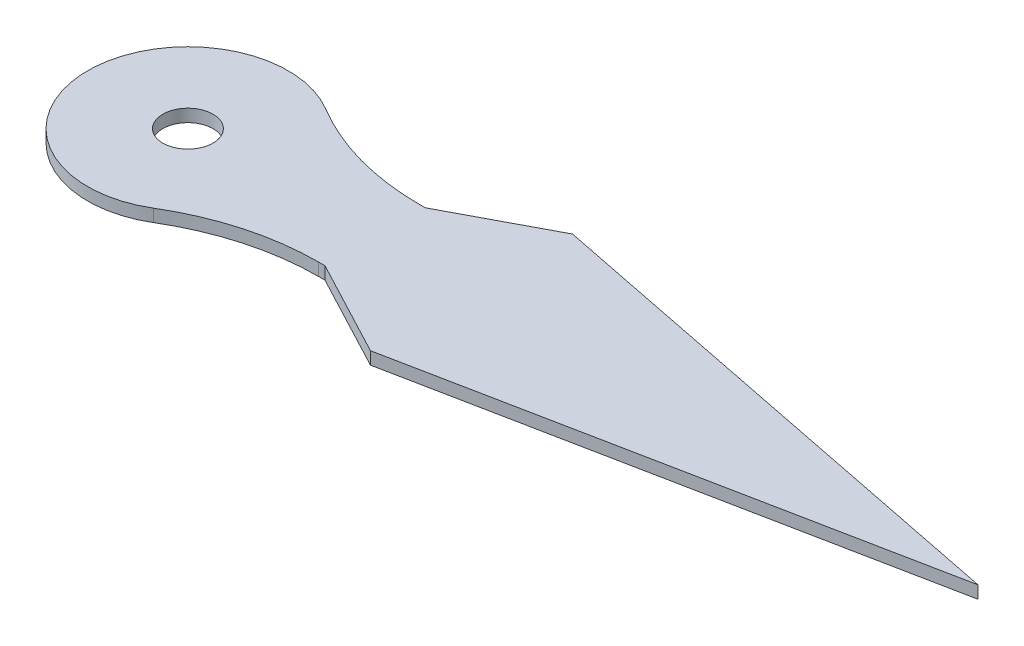
SolidWorks part; units mm, degrees
ref_plane "Front Plane" through (0, 0, 0) normal (0, 0, 1) x (1, 0, 0)
ref_plane "Top Plane" through (0, 0, 0) normal (0, 1, 0) x (1, 0, 0)
ref_plane "Right Plane" through (0, 0, 0) normal (1, 0, 0) x (0, 0, -1)
sketch "Sketch1" plane through (0, 0, 0) normal (0, 1, 0) x (1, 0, 0)
  line L3 (3.4641, 2) -> (7.4641, 2)
  line L4 (11.3026, -4.0272) -> (31.4929, 0)
  line L5 (7.4641, 2) -> (11.3026, 4.0272)
  line L6 (11.3026, 4.0272) -> (31.4929, 0)
  line L7 (7.4641, -2) -> (11.3026, -4.0272)
  line L8 (3.4641, -2) -> (7.4641, -2)
  circle A0 centre (0, 0) radius 4
  dimension "D3" = 4
extrude "Boss-Extrude2" add sketch "Sketch1" along normal blind 0.5 contours A0 L8 L7 L4 L6 L5 L3 | A0
fillet "Fillet1" radius 10 2 edges at (3.4641, 0.25, -2) (3.4641, 0.25, 2)
sketch "Sketch3" plane through (0, 0.5, 0) normal (0, 1, 0) x (1, 0, 0)
  circle A0 centre (0, 0) radius 1
extrude "Cut-Extrude2" cut sketch "Sketch3" against normal through all
